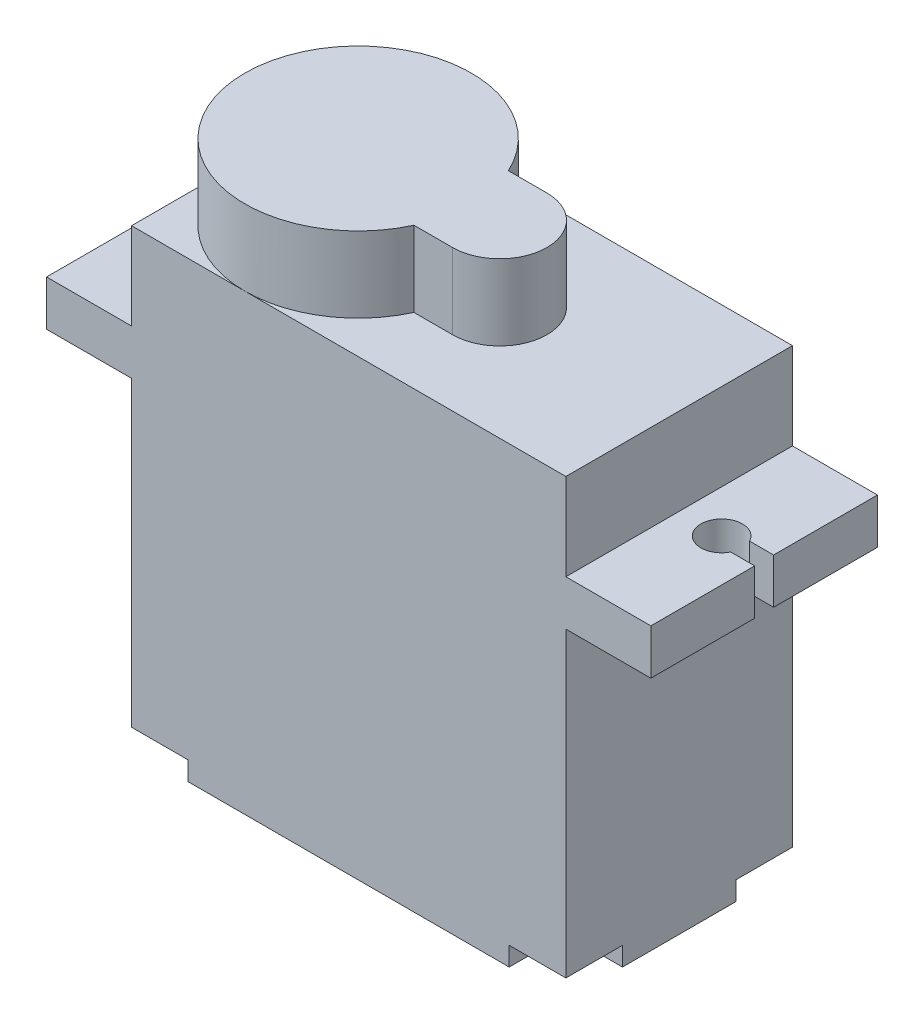
SolidWorks part; units mm, degrees
ref_plane "Ön Düzlem" through (0, 0, 0) normal (0, 0, 1) x (1, 0, 0)
ref_plane "Üst Düzlem" through (0, 0, 0) normal (0, 1, 0) x (1, 0, 0)
ref_plane "Sağ Düzlem" through (0, 0, 0) normal (1, 0, 0) x (0, 0, -1)
sketch "Çizim1" plane through (0, 0, 0) normal (0, 1, 0) x (1, 0, 0)
  line L1 (-11.5, 6) -> (11.5, 6)
  line L2 (-11.5, 6) -> (-11.5, -6)
  line L3 (-11.5, -6) -> (11.5, -6)
  line L4 (11.5, 6) -> (11.5, -6)
  line L5 (-11.5, 6) -> (11.5, -6) construction
  line L6 (-11.5, -6) -> (11.5, 6) construction
  point P0 (0, 0)
  dimension "D1" = 23
  dimension "D2" = 12
extrude "Yükseklik-Ekstrüzyon1" add sketch "Çizim1" along normal blind 24
ref_plane "Düzlem1" through (0, 17, 0) normal (0, -1, 0) x (-1, 0, 0)
sketch "Çizim2" plane through (0, 17, 0) normal (0, -1, 0) x (-1, 0, 0)
  line L0 (-11.5, 6) -> (11.5, 6) construction
  line L1 (-16, 6) -> (16, 6)
  line L2 (-16, 6) -> (-16, 0.5)
  line L3 (-16, -6) -> (16, -6)
  line L4 (16, 6) -> (16, 0.5)
  line L5 (-16, 6) -> (16, -6) construction
  line L6 (-16, -6) -> (16, 6) construction
  line L7 (-16, 0.5) -> (-14.7298, 0.5)
  line L8 (-16, -0.5) -> (-14.7298, -0.5)
  line L9 (0, 0) -> (0, 6) construction
  line L10 (16, -0.5) -> (14.7298, -0.5)
  line L11 (16, 0.5) -> (14.7298, 0.5)
  line L12 (-16, -0.5) -> (-16, -6)
  line L13 (16, -0.5) -> (16, -6)
  arc A0 (-14.7298, -0.5) -> (-14.7298, 0.5) centre (-13.75, 0) ccw
  arc A1 (14.7298, 0.5) -> (14.7298, -0.5) centre (13.75, 0) ccw
  point P0 (0, 0)
  dimension "D2" = 2.2
  dimension "D3" = 27.5
  dimension "D1" = 32
  dimension "D5" = 1
  dimension "D6" = 0.5
extrude "Yükseklik-Ekstrüzyon2" add sketch "Çizim2" against normal blind 2.4
sketch "Çizim3" plane through (0, 24, 0) normal (0, 1, 0) x (1, 0, 0)
  line L0 (11.5, 6) -> (-11.5, 6) construction
  line L1 (-11.5, -6) -> (11.5, -6) construction
  line L2 (-11.5, 6) -> (-11.5, -6) construction
  line L3 (2, -2.5) -> (-0.0456, -2.5)
  line L4 (2, 2.5) -> (-0.0456, 2.5)
  arc A0 (-0.0456, 2.5) -> (-0.0456, -2.5) centre (-5.5, 0) ccw
  arc A1 (2, -2.5) -> (2, 2.5) centre (2, 0) ccw
  dimension "D1" = 5
  dimension "D2" = 7.5
extrude "Yükseklik-Ekstrüzyon3" add sketch "Çizim3" along normal blind 4
sketch "Çizim4" plane through (0, 0, 0) normal (0, -1, 0) x (1, 0, 0)
  line L2 (0, -6) -> (0, 6) construction
  line L3 (-11.5, 6) -> (-8.5, 6)
  line L4 (-11.5, 6) -> (-11.5, 3)
  line L5 (-11.5, 3) -> (-10, 3)
  line L6 (-8.5, 6) -> (-8.5, 4.5)
  line L7 (-11.5, -6) -> (-8.5, -6)
  line L8 (-11.5, -6) -> (-11.5, -3)
  line L9 (-11.5, -3) -> (-10, -3)
  line L10 (-8.5, -6) -> (-8.5, -4.5)
  line L11 (11.5, -6) -> (-11.5, -6) construction
  line L12 (-11.5, 6) -> (11.5, 6) construction
  line L13 (11.5, 3) -> (10, 3)
  line L14 (8.5, 6) -> (8.5, 4.5)
  line L15 (11.5, 6) -> (8.5, 6)
  line L16 (11.5, 6) -> (11.5, 3)
  line L17 (11.5, -3) -> (10, -3)
  line L18 (8.5, -6) -> (8.5, -4.5)
  line L19 (11.5, -6) -> (8.5, -6)
  line L20 (11.5, -6) -> (11.5, -3)
  arc A0 (-10, 3) -> (-8.5, 4.5) centre (-10, 4.5) ccw
  arc A1 (-10, -3) -> (-8.5, -4.5) centre (-10, -4.5) cw
  arc A2 (10, 3) -> (8.5, 4.5) centre (10, 4.5) cw
  arc A3 (10, -3) -> (8.5, -4.5) centre (10, -4.5) ccw
  dimension "D1" = 3
  dimension "D5" = 1.5
  dimension "D2" = 3
  dimension "D3" = 3
  dimension "D4" = 3
extrude "Kes-Ekstrüzyon1" cut sketch "Çizim4" against normal blind 1
sketch "Çizim5" plane through (0, 0, 0) normal (0, -1, 0) x (1, 0, 0)
  line L0 (-11.5, -3) -> (-11.5, 3) construction
  line L1 (-11.5, 1.75) -> (-9, 1.75)
  line L2 (-11.5, 1.75) -> (-11.5, -1.75)
  line L3 (-11.5, -1.75) -> (-9, -1.75)
  line L4 (-9, 1.75) -> (-9, -1.75)
  dimension "D1" = 3.5
  dimension "D2" = 1.75
  dimension "D3" = 2.5
extrude "Kes-Ekstrüzyon2" cut sketch "Çizim5" against normal blind 1
sketch "Çizim6" plane through (0, 1, 0) normal (0, -1, 0) x (1, 0, 0)
  line L0 (-9, 1.75) -> (-11.5, 1.75) construction
  line L1 (-11, 1.75) -> (-9, 1.75)
  line L2 (-11, 1.75) -> (-11, -1.75)
  line L3 (-11, -1.75) -> (-9, -1.75)
  line L4 (-9, 1.75) -> (-9, -1.75)
  line L5 (-11.5, 6) -> (-11.5, -6) construction
  dimension "D1" = 0.5
extrude "Kes-Ekstrüzyon3" cut sketch "Çizim6" against normal blind 3
chamfer "Pah1" distance 2 angle 26.5 2 edges at (-11.5, 0, 2.375) (-11.5, 0, -2.375)
